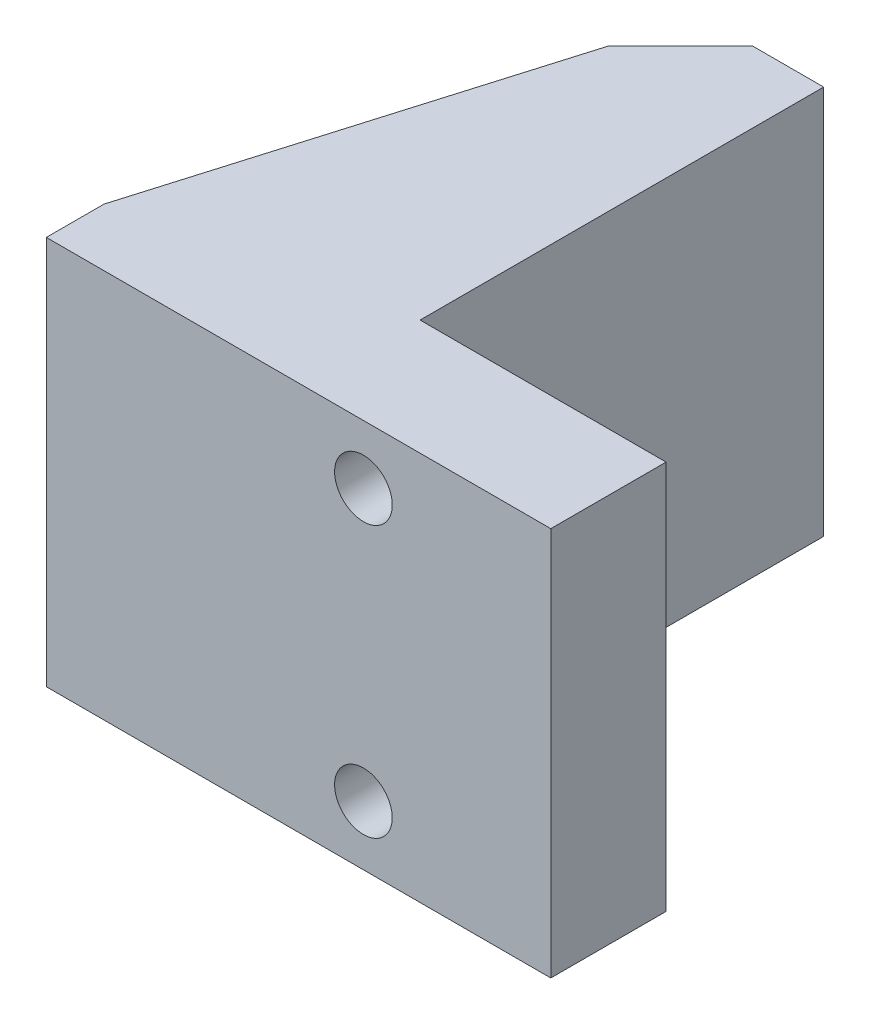
SolidWorks part; units mm, degrees
ref_plane "Front Plane" through (0, 0, 0) normal (0, 0, 1) x (1, 0, 0)
ref_plane "Top Plane" through (0, 0, 0) normal (0, 1, 0) x (1, 0, 0)
ref_plane "Right Plane" through (0, 0, 0) normal (1, 0, 0) x (0, 0, -1)
sketch "Sketch1" plane through (0, 0, 0) normal (0, 0, 1) x (1, 0, 0)
  line L1 (0, 0) -> (17.145, 0)
  line L2 (0, 0) -> (0, -17.145)
  line L3 (0, -17.145) -> (17.145, -17.145)
  line L4 (17.145, 0) -> (17.145, -17.145)
  dimension "D1" = 17.145
  dimension "D2" = 17.145
extrude "Boss-Extrude1" add sketch "Sketch1" along normal blind 5.08
sketch "Sketch2" plane through (0, 0, 0) normal (0, 0, -1) x (-1, 0, 0)
  line L0 (-8.89, 0) -> (-8.89, -17.145) construction
  line L1 (-17.145, 0) -> (0, 0) construction
  line L2 (0, -17.145) -> (-17.145, -17.145) construction
  line L3 (0, 0) -> (0, -17.145) construction
  circle A0 centre (-8.89, -2.5908) radius 1.27
  circle A1 centre (-8.89, -14.5288) radius 1.27
  dimension "D1" = 11.938
  dimension "D2" = 2.54
  dimension "D3" = 2.54
  dimension "D4" = 2.6162
  dimension "D5" = 2.5908
  dimension "D6" = 8.89
extrude "Cut-Extrude1" cut sketch "Sketch2" against normal through all
sketch "Sketch3" plane through (0, 0, 0) normal (0, 0, -1) x (-1, 0, 0)
  circle A0 centre (-8.89, -2.5908) radius 2.54
  circle A1 centre (-8.89, -14.5288) radius 2.54
  dimension "D1" = 5.08
  dimension ".2" = 5.08
extrude "Cut-Extrude4" cut sketch "Sketch3" against normal blind 2.54
sketch "Sketch4" plane through (0, 0, 0) normal (0, 0, -1) x (-1, 0, 0)
  line L0 (0, -17.145) -> (-17.145, -17.145) construction
  line L1 (0, 0) -> (-6.3077, 0)
  line L2 (0, 0) -> (0, -17.145)
  line L3 (0, -17.145) -> (-6.3077, -17.145)
  line L4 (-6.3077, 0) -> (-6.3077, -17.145)
extrude "Boss-Extrude2" add sketch "Sketch4" along normal blind 17.78
sketch "Sketch5" plane through (0, 0, 0) normal (-1, 0, 0) x (0, 0, 1)
  line L0 (5.08, -17.145) -> (-17.78, -17.145) construction
  line L1 (5.08, 0) -> (2.54, 0)
  line L2 (5.08, 0) -> (5.08, -17.145)
  line L3 (5.08, -17.145) -> (2.54, -17.145)
  line L4 (2.54, 0) -> (2.54, -17.145)
  dimension "D1" = 2.54
extrude "Boss-Extrude3" add sketch "Sketch5" along normal blind 5.08
chamfer "Chamfer1" distance 3.175 angle 45 1 edges at (0, -8.5725, -17.78)
sketch "Sketch7" plane through (0, 0, 0) normal (0, 1, 0) x (1, 0, 0)
  line L0 (-5.08, -2.54) -> (0, 14.605)
  line L1 (0, 14.605) -> (0, -2.54)
  line L2 (0, -2.54) -> (-5.08, -2.54)
extrude "Boss-Extrude4" add sketch "Sketch7" against normal blind 2.54
sketch "Sketch8" plane through (0, -17.145, 0) normal (0, -1, 0) x (1, 0, 0)
  line L3 (0, 2.54) -> (-5.08, 2.54)
  line L4 (-5.08, 2.54) -> (0, -14.605)
  line L5 (0, -14.605) -> (0, 2.54)
  line L6 (0, 2.54) -> (-5.08, 2.54)
  line L7 (-5.08, 2.54) -> (0, -14.605)
  line L8 (0, -14.605) -> (0, 2.54)
  dimension "D1" = 0
extrude "Boss-Extrude5" add sketch "Sketch8" against normal blind 2.54
